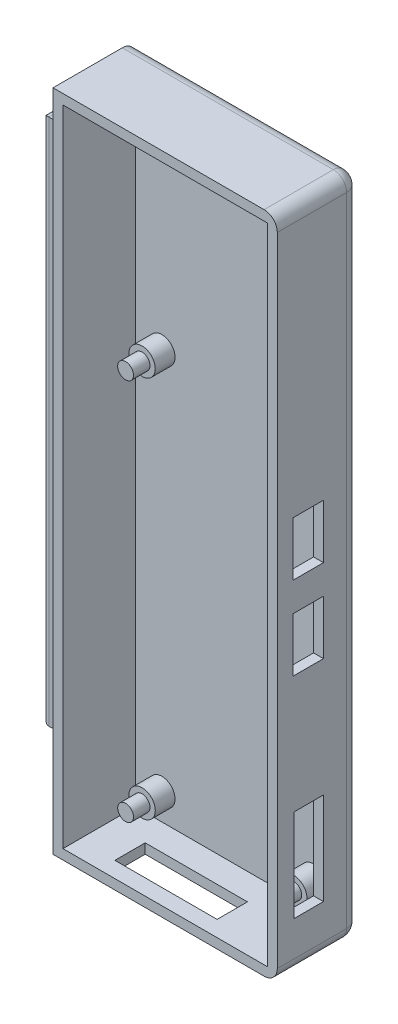
SolidWorks part; units mm, degrees
ref_plane "Plan de face" through (0, 0, 0) normal (0, 0, 1) x (1, 0, 0)
ref_plane "Plan de dessus" through (0, 0, 0) normal (0, 1, 0) x (1, 0, 0)
ref_plane "Plan de droite" through (0, 0, 0) normal (1, 0, 0) x (0, 0, -1)
sketch "Esquisse1" plane through (0, 0, 0) normal (0, 0, 1) x (1, 0, 0)
  line L1 (0, 0) -> (34, 0)
  line L2 (0, 0) -> (0, 100.65)
  line L3 (0, 100.65) -> (34, 100.65)
  line L4 (34, 0) -> (34, 100.65)
  dimension "D1" = 100.65
  dimension "D2" = 34
extrude "Boss.-Extru.1" add sketch "Esquisse1" along normal blind 12.5
sketch "Esquisse2" plane through (0, 0, 12.5) normal (0, 0, 1) x (1, 0, 0)
  line L0 (0, 100.65) -> (0, 0) construction
  line L1 (1.5, 99.15) -> (32.5, 99.15)
  line L2 (1.5, 99.15) -> (1.5, 1.5)
  line L3 (1.5, 1.5) -> (32.5, 1.5)
  line L4 (32.5, 99.15) -> (32.5, 1.5)
  line L5 (34, 0) -> (34, 100.65) construction
  line L6 (0, 0) -> (34, 0) construction
  line L7 (34, 100.65) -> (0, 100.65) construction
  dimension "D1" = 1.5
  dimension "D2" = 1.5
  dimension "D3" = 1.5
  dimension "D4" = 1.5
extrude "Enlèv. mat.-Extru.1" cut sketch "Esquisse2" against normal blind 11 contours L2 L1 L4 L3
sketch "RASP" plane through (0, 0, 1.5) normal (0, 0, 1) x (1, 0, 0)
  line L0 (1.5, 99.15) -> (1.5, 1.5) construction
  line L1 (2, 67) -> (32, 67)
  line L2 (2, 67) -> (2, 2)
  line L3 (2, 2) -> (32, 2)
  line L4 (32, 67) -> (32, 2)
  line L6 (1.5, 1.5) -> (32.5, 1.5) construction
  circle A0 centre (5.5, 5.5) radius 1.375
  circle A1 centre (28.5, 5.5) radius 1.375
  circle A2 centre (5.5, 63.5) radius 1.375
  circle A3 centre (28.5, 63.5) radius 1.375
  point P16 (32, 56)
  point P17 (32, 43.4)
  dimension "D5" = 2.75
  dimension "D6" = 2.75
  dimension "D11" = 2.75
  dimension "D12" = 2.75
  dimension "D1" = 30
  dimension "D2" = 65
  dimension "D3" = 0.5
  dimension "D4" = 0.5
  dimension "D7" = 23
  dimension "D8" = 3.5
  dimension "D9" = 3.5
  dimension "D10" = 3.5
  dimension "D13" = 23
  dimension "D14" = 3.5
  dimension "D15" = 3.5
  dimension "D16" = 3.5
  dimension "D17" = 54
  dimension "D18" = 41.4
sketch "Esquisse5" plane through (0, 0, 1.5) normal (0, 0, 1) x (1, 0, 0)
  circle A0 centre (5.5, 63.5) radius 2
  circle A1 centre (28.5, 63.5) radius 2
  circle A2 centre (5.5, 5.5) radius 2
  circle A3 centre (28.5, 5.5) radius 2
  dimension "D1" = 4
  dimension "D2" = 4
  dimension "D3" = 4
  dimension "D4" = 4
extrude "Boss.-Extru.4" add sketch "Esquisse5" along normal blind 3
sketch "Esquisse6" plane through (0, 0, 1.5) normal (0, 0, 1) x (1, 0, 0)
  circle A0 centre (5.5, 63.5) radius 1.2
  circle A1 centre (28.5, 63.5) radius 1.2
  circle A2 centre (5.5, 5.5) radius 1.2
  circle A3 centre (28.5, 5.5) radius 1.2
  dimension "D1" = 2.4
  dimension "D2" = 2.4
  dimension "D3" = 2.4
  dimension "D4" = 2.4
extrude "Boss.-Extru.5" add sketch "Esquisse6" along normal blind 5.5
fillet "Congé2" radius 2 1 edges at (34, 0, 6.25)
fillet "Congé3" radius 2 1 edges at (34, 100.65, 6.25)
fillet "Congé4" radius 2 5 edges at (16, 0, 0) (33.4142, 0.5858, 0) (16, 100.65, 0) (33.4142, 100.0642, 0) (34, 50.325, 0)
sketch "Esquisse7" plane through (0, 0, 0) normal (-1, 0, 0) x (0, 0, 1)
  line L0 (0, 98.65) -> (0, 2) construction
  line L1 (3.25, 95.45) -> (10.75, 95.45)
  line L2 (3.25, 95.45) -> (3.25, 15.45)
  line L3 (3.25, 15.45) -> (10.75, 15.45)
  line L4 (10.75, 95.45) -> (10.75, 15.45)
  line L5 (12.5, 100.65) -> (2, 100.65) construction
  dimension "D1" = 3.25
  dimension "D2" = 5.2
  dimension "D3" = 7.5
  dimension "D4" = 80
extrude "Boss.-Extru.6" add sketch "Esquisse7" along normal blind 1
sketch "Esquisse9" plane through (-1, 0, 0) normal (-1, 0, 0) x (0, 0, 1)
  line L0 (3.25, 95.45) -> (3.25, 15.45) construction
  line L1 (2, 95.45) -> (11.45, 95.45)
  line L2 (2, 95.45) -> (2, 15.45)
  line L3 (2, 15.45) -> (11.45, 15.45)
  line L4 (11.45, 95.45) -> (11.45, 15.45)
  line L5 (10.75, 95.45) -> (3.25, 95.45) construction
  dimension "D1" = 80
  dimension "D2" = 0
  dimension "D3" = 9.45
  dimension "D4" = 1.25
extrude "Boss.-Extru.7" add sketch "Esquisse9" along normal blind 1.7
sketch "Esquisse10" plane through (32.5, 0, 0) normal (-1, 0, 0) x (0, 0, 1)
  line L0 (1.5, 99.15) -> (1.5, 1.5) construction
  line L1 (10.1, 60) -> (5.5, 60)
  line L2 (10.1, 60) -> (10.1, 51.8)
  line L3 (10.1, 51.8) -> (5.5, 51.8)
  line L4 (5.5, 60) -> (5.5, 51.8)
  line L5 (10.1, 47.4) -> (5.5, 47.4)
  line L6 (10.1, 47.4) -> (10.1, 39.2)
  line L7 (10.1, 39.2) -> (5.5, 39.2)
  line L8 (5.5, 47.4) -> (5.5, 39.2)
  line L9 (10, 21.3) -> (5.5, 21.3)
  line L10 (10, 21.3) -> (10, 7.3)
  line L11 (10, 7.3) -> (5.5, 7.3)
  line L12 (5.5, 21.3) -> (5.5, 7.3)
  dimension "D1" = 4
  dimension "D2" = 4
  dimension "D3" = 4
  dimension "D4" = 14
  dimension "D5" = 8.2
  dimension "D6" = 8.2
  dimension "D7" = 4.4
  dimension "D8" = 17.9
  dimension "D9" = 4.5
  dimension "D10" = 4.6
  dimension "D11" = 4.6
  dimension "D12" = 0.6
extrude "Enlèv. mat.-Extru.2" cut sketch "Esquisse10" against normal blind 3
sketch "Esquisse11" plane through (0, 1.5, 0) normal (0, 1, 0) x (1, 0, 0)
  line L0 (1.5, -1.5) -> (32.5, -1.5) construction
  line L1 (22.4742, -10.1) -> (6.9742, -10.1)
  line L2 (22.4742, -10.1) -> (22.4742, -5.5)
  line L3 (22.4742, -5.5) -> (6.9742, -5.5)
  line L4 (6.9742, -10.1) -> (6.9742, -5.5)
  dimension "D1" = 15.5
  dimension "D2" = 4.6
  dimension "D3" = 4
extrude "Enlèv. mat.-Extru.3" cut sketch "Esquisse11" against normal blind 3 contours L2 L1 L4 L3
fillet "Congé7" radius 1 4 edges at (-2.7, 95.45, 6.725) (-2.7, 55.45, 2) (-2.7, 15.45, 6.725) (-2.7, 55.45, 11.45)
